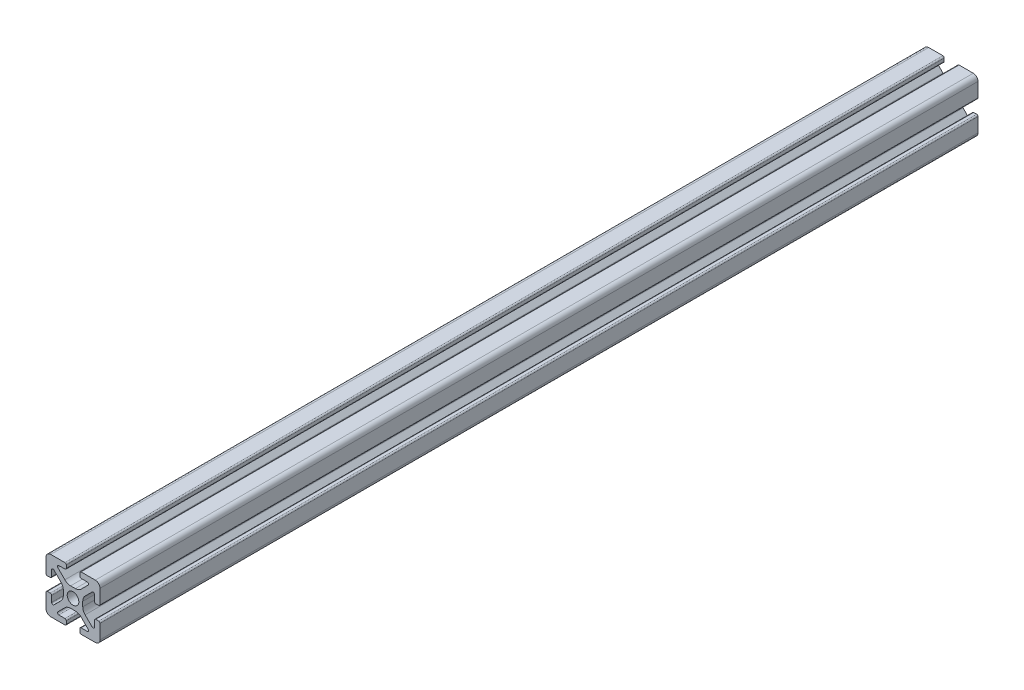
SolidWorks part; units mm, degrees
material "6061 Alloy"
ref_plane "Front Plane" through (0, 0, 0) normal (0, 0, 1) x (1, 0, 0)
ref_plane "Top Plane" through (0, 0, 0) normal (0, 1, 0) x (1, 0, 0)
ref_plane "Right Plane" through (0, 0, 0) normal (1, 0, 0) x (0, 0, -1)
sketch "Sketch2" plane through (0, 0, 0) normal (0, 0, 1) x (1, 0, 0)
  line L0 (0, 10) -> (0, -10) construction
  line L1 (-10, 0) -> (10, 0) construction
  line L2 (2.5, -10) -> (10, -10)
  line L3 (10, -10) -> (10, -2.5)
  line L4 (2.5, -10) -> (2.5, -7.9246)
  line L5 (2.5, -7.9246) -> (6.4571, -7.9246)
  line L6 (6.4571, -7.9246) -> (2.1325, -3.6)
  line L7 (0, 0) -> (10, -10) construction
  line L8 (10, -2.5) -> (7.9246, -2.5)
  line L9 (7.9246, -2.5) -> (7.9246, -6.4571)
  line L10 (7.9246, -6.4571) -> (3.6, -2.1325)
  line L11 (5.7623, -4.2948) -> (4.2948, -5.7623) construction
  circle A0 centre (0, 0) radius 2.15
  arc A1 (5.25, -7.9246) -> (5.6036, -7.0711) centre (5.25, -7.4246) ccw construction
  point P8 (0, -3.6)
  point P16 (5.0286, -5.0286)
  dimension "Center Hole Diameter" = 4.3
  dimension "D3" = 0.5
  dimension "Rail Height" = 20
  dimension "Rail Width" = 20
  dimension "T-Slot Width" = 5
  dimension "Slot Depth" = 6.4
  dimension "Slot Inner Width" = 11.5
sketch "Sketch3" plane through (0, 0, 0) normal (1, 0, 0) x (0, 0, -1)
  line L0 (-152.4, -10) -> (152.4, -10) construction
  line L1 (-127, 0) -> (127, 0) construction
  line L2 (0, 10) -> (0, -10) construction
  line L3 (0, 10) -> (0, -10) construction
  point P6 (-127, 0)
  point P8 (127, 0)
  dimension "Length" = 304.8
  dimension "D1" = 25.4
sketch "Sketch4" plane through (0, 0, 0) normal (0, 0, 1) x (1, 0, 0)
  line L0 (3, -10) -> (8.25, -10)
  line L1 (2.5, -10) -> (10, -10) construction
  line L2 (2.5, -10) -> (2.5, -7.9246) construction
  line L3 (2.5, -7.9246) -> (6.4571, -7.9246) construction
  line L4 (2.5, -8.4246) -> (2.5, -9.5)
  line L5 (3, -7.9246) -> (5.25, -7.9246)
  line L6 (0, -3.6) -> (0.8898, -3.6)
  line L7 (6.4571, -7.9246) -> (2.1325, -3.6) construction
  line L8 (3.0112, -4.4787) -> (5.6036, -7.0711)
  line L9 (10, -10) -> (10, -2.5) construction
  line L10 (7.9246, -6.4571) -> (3.6, -2.1325) construction
  line L11 (7.9246, -2.5) -> (7.9246, -6.4571) construction
  line L12 (7.9246, -5.25) -> (7.9246, -3)
  line L13 (10, -2.5) -> (7.9246, -2.5) construction
  line L14 (8.4246, -2.5) -> (9.5, -2.5)
  line L15 (10, -3) -> (10, -8.25)
  line L16 (7.0711, -5.6036) -> (4.4787, -3.0112)
  line L17 (3.6, 0) -> (3.6, -0.8898)
  line L18 (-10, 0) -> (10, 0) construction
  line L19 (0, -3.6) -> (0, -2.15)
  line L20 (0, 10) -> (0, -10) construction
  line L21 (3.6, 0) -> (2.15, 0)
  arc A0 (2.5, -9.5) -> (3, -10) centre (3, -9.5) ccw
  arc A1 (5.25, -7.9246) -> (5.6036, -7.0711) centre (5.25, -7.4246) ccw construction
  arc A2 (2.5, -8.4246) -> (3, -7.9246) centre (3, -8.4246) cw
  arc A3 (5.25, -7.9246) -> (5.6036, -7.0711) centre (5.25, -7.4246) ccw
  arc A4 (0.8898, -3.6) -> (3.0112, -4.4787) centre (0.8898, -6.6) cw
  arc A5 (8.25, -10) -> (10, -8.25) centre (8.25, -8.25) ccw
  arc A6 (7.0711, -5.6036) -> (7.9246, -5.25) centre (7.4246, -5.25) ccw
  arc A7 (7.9246, -3) -> (8.4246, -2.5) centre (8.4246, -3) cw
  arc A8 (9.5, -2.5) -> (10, -3) centre (9.5, -3) cw
  arc A9 (4.4787, -3.0112) -> (3.6, -0.8898) centre (6.6, -0.8898) cw
  circle A10 centre (0, 0) radius 2.15 construction
  arc A11 (0, -2.15) -> (2.15, 0) centre (0, 0) ccw
  dimension "D1" = 1.75
  dimension "D2" = 3
extrude "Boss-Extrude1" add sketch "Sketch4" along normal mid plane 325
mirror "Mirror1" about plane through (0, 0, 0) normal (1, 0, 0) of bodies 134
mirror "Mirror2" about plane through (0, 0, 0) normal (0, 1, 0) of bodies 135
equation "\"D3@Sketch2\"=\"T-Slot Width@Sketch2\"*0.1"
equation "\"D1@Sketch4\"=\"D3@Sketch2\"*3.5"
equation "\"D2@Sketch4\"=\"D3@Sketch2\"*6"
equation "\"D1@Boss-Extrude1\"=\"Length@Sketch3\""
